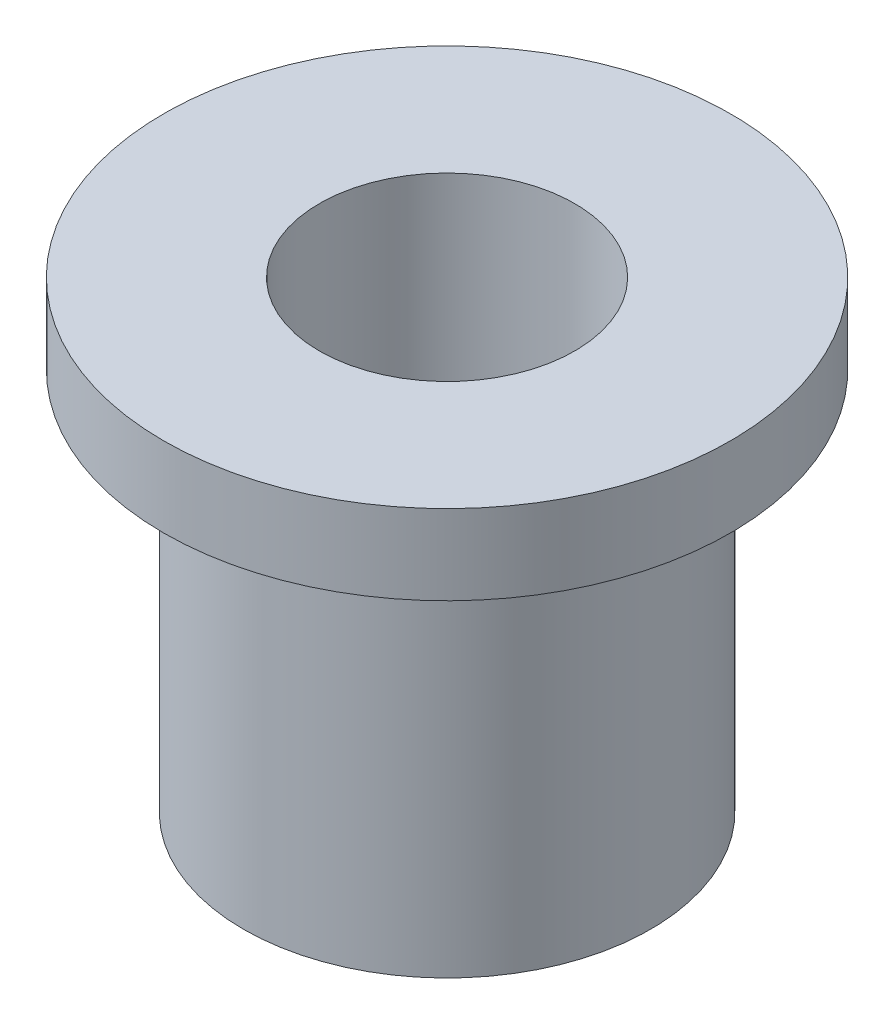
SolidWorks part; units mm, degrees
ref_plane "Front Plane" through (0, 0, 0) normal (0, 0, 1) x (1, 0, 0)
ref_plane "Top Plane" through (0, 0, 0) normal (0, 1, 0) x (1, 0, 0)
ref_plane "Right Plane" through (0, 0, 0) normal (1, 0, 0) x (0, 0, -1)
sketch "Sketch1" plane through (0, 0, 0) normal (0, 1, 0) x (1, 0, 0)
  circle A0 centre (0, 0) radius 2.55
  circle A1 centre (0, 0) radius 1.6
  dimension "D1" = 5.1
  dimension "D2" = 3.2
extrude "Boss-Extrude1" add sketch "Sketch1" along normal blind 5.8
sketch "Sketch2" plane through (0, 5.8, 0) normal (0, 1, 0) x (1, 0, 0)
  circle A0 centre (0, 0) radius 1.6
  circle A1 centre (0, 0) radius 3.55
  circle A2 centre (0, 0) radius 2.55 construction
  dimension "D1" = 1
extrude "Boss-Extrude2" add sketch "Sketch2" against normal blind 1
